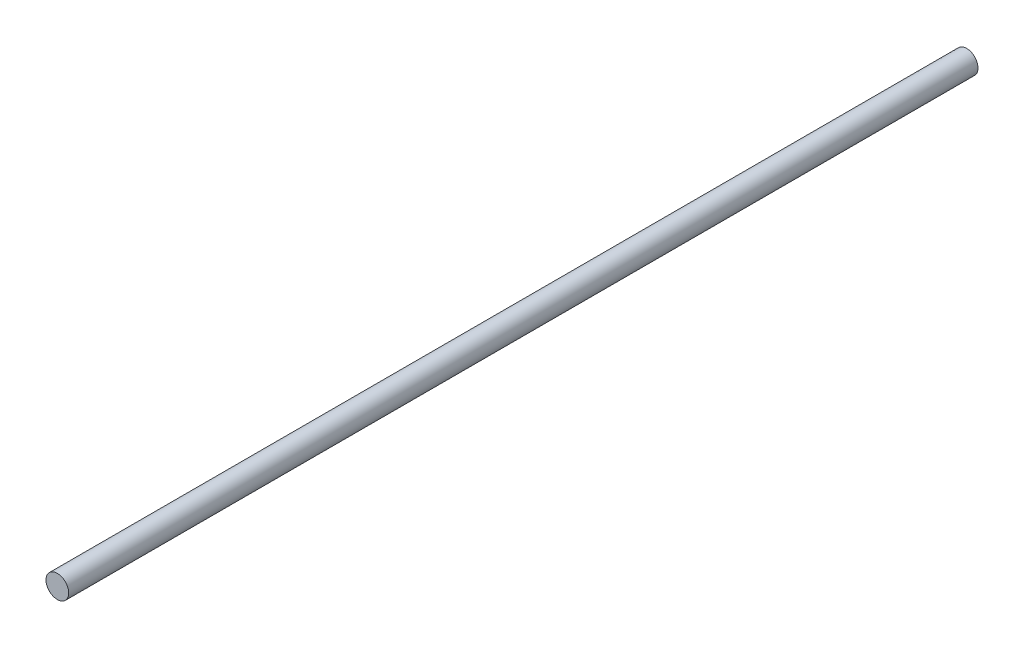
SolidWorks part; units mm, degrees
ref_plane "Front Plane" through (0, 0, 0) normal (0, 0, 1) x (1, 0, 0)
ref_plane "Top Plane" through (0, 0, 0) normal (0, 1, 0) x (1, 0, 0)
ref_plane "Right Plane" through (0, 0, 0) normal (1, 0, 0) x (0, 0, -1)
sketch "Sketch1" plane through (0, 0, 0) normal (0, 0, 1) x (1, 0, 0)
  circle A0 centre (0, 0) radius 5
  dimension "D1" = 10
extrude "Boss-Extrude1" add sketch "Sketch1" along normal blind 400
